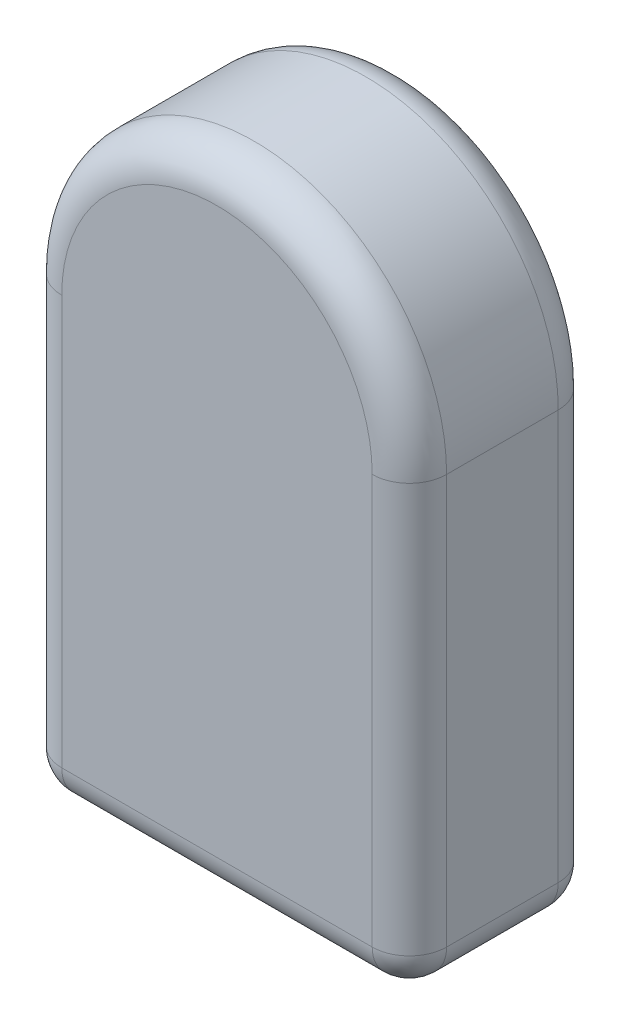
SolidWorks part; units mm, degrees
ref_plane "Front Plane" through (0, 0, 0) normal (0, 0, 1) x (1, 0, 0)
ref_plane "Top Plane" through (0, 0, 0) normal (0, 1, 0) x (1, 0, 0)
ref_plane "Right Plane" through (0, 0, 0) normal (1, 0, 0) x (0, 0, -1)
sketch "Sketch1" plane through (0, 0, 0) normal (0, 0, 1) x (1, 0, 0)
  line L0 (-9.132, 0) -> (-9.132, 12)
  line L1 (55, 0) -> (-55, 0) construction
  line L3 (1.2106, 12) -> (1.2106, 0)
  line L4 (1.2106, 0) -> (-9.132, 0)
  arc A0 (-9.132, 12) -> (1.2106, 12) centre (-3.9607, 12) cw
extrude "Boss-Extrude1" add sketch "Sketch1" along normal blind 5
fillet "Fillet2" radius 1 10 edges at (1.2106, 0, 2.5) (-3.9607, 17.1713, 0) (-3.9607, 17.1713, 5) (1.2106, 6, 0) (1.2106, 6, 5) (-3.9607, 0, 5) (-3.9607, 0, 0) (-9.132, 0, 2.5) (-9.132, 6, 5) (-9.132, 6, 0)
